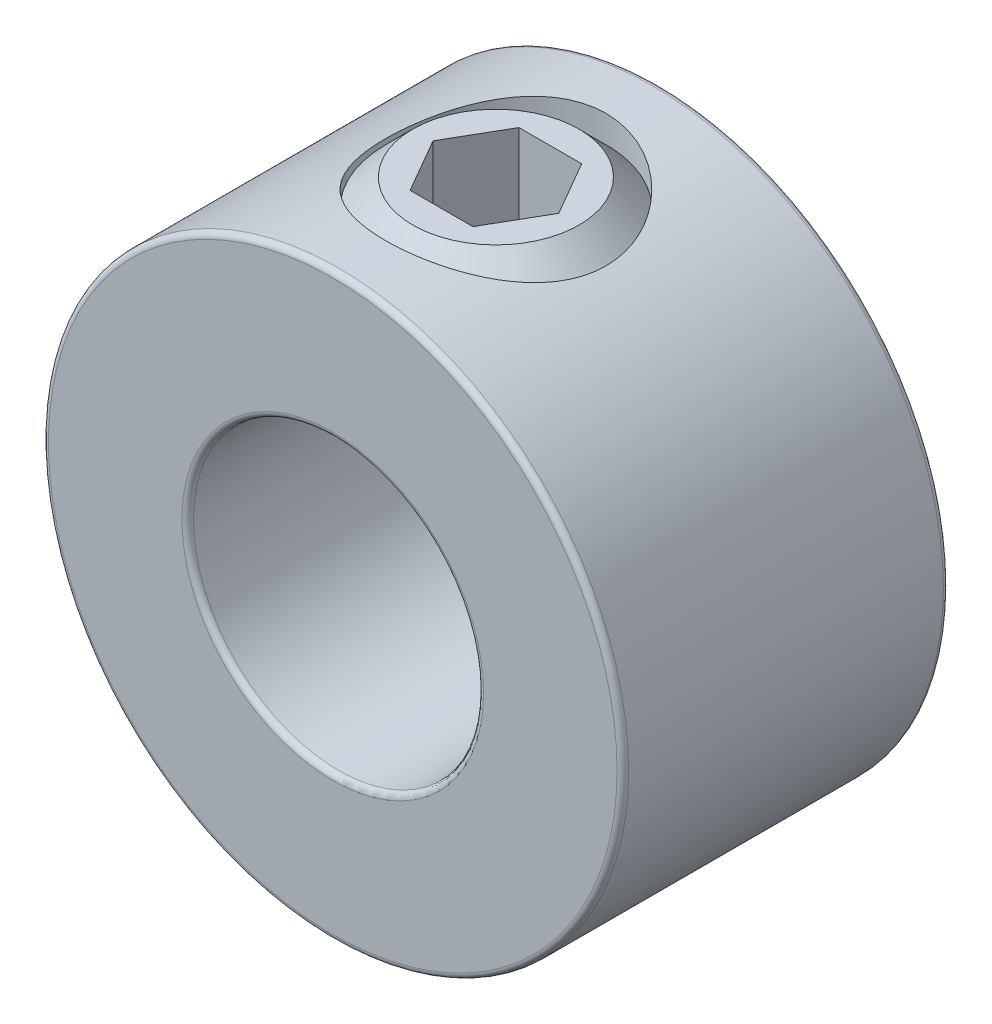
SolidWorks part; units mm, degrees
ref_plane "Front Plane" through (0, 0, 0) normal (0, 0, 1) x (1, 0, 0)
ref_plane "Top Plane" through (0, 0, 0) normal (0, 1, 0) x (1, 0, 0)
ref_plane "Right Plane" through (0, 0, 0) normal (1, 0, 0) x (0, 0, -1)
sketch "Sketch1" plane through (0, 0, 0) normal (0, 0, 1) x (1, 0, 0)
  circle A0 centre (0, 0) radius 6.35
  circle A1 centre (0, 0) radius 3.175
  point P4 (6.35, 0)
  dimension "Bore Dia" = 6.35
  dimension "OD" = 12.7
extrude "Extrude1" add sketch "Sketch1" along normal mid plane 7.1437
sketch "Sketch2" plane through (41.275, 0, 0) normal (0, -1, 0) x (0, 0, -1)
  line L0 (3.5719, -41.275) -> (-3.5719, -41.275) construction
  line L1 (-3.5719, -34.925) -> (-3.5719, -47.625) construction
  line L2 (3.5719, -47.625) -> (3.5719, -34.925) construction
  circle A0 centre (0, -41.275) radius 2.413
  point P7 (0, -43.688)
  dimension "Set Screw Dia" = 4.826
extrude "Cut-Extrude1" cut sketch "Sketch2" against normal through all
fillet "Fillet1" radius 0.127 4 edges at (3.175, 0, -3.5719) (3.175, 0, 3.5719) (6.35, 0, -3.5719) (6.35, 0, 3.5719)
sketch "Sketch3" plane through (0, 0, 0) normal (0, 0, 1) x (1, 0, 0)
  line L0 (-1.8198, 3.175) -> (-0.7119, 3.175)
  line L1 (0, 3.8869) -> (-0.7119, 3.175)
  line L2 (0, 3.8869) -> (0, 6.35)
  line L3 (0, 6.35) -> (-1.8198, 6.35)
  line L4 (-2.413, 3.7682) -> (-2.413, 5.7568)
  line L5 (0, 3.175) -> (0, 0) construction
  line L6 (-2.413, 3.7682) -> (-2.413, 3.175) construction
  line L7 (-2.413, 3.175) -> (-1.8198, 3.175) construction
  line L8 (-2.413, 5.7568) -> (-2.413, 6.35) construction
  line L9 (-1.8198, 3.175) -> (-2.413, 3.7682)
  line L10 (-2.413, 5.7568) -> (-1.8198, 6.35)
  line L11 (-2.413, 6.35) -> (-1.8198, 6.35) construction
  line L12 (-0.7119, 3.175) -> (0, 3.175) construction
  line L13 (0, 3.175) -> (0, 3.8869) construction
  circle A1 centre (0, 0) radius 3.175 construction
  dimension "D1" = 0.7119
  dimension "D2" = 0.5932
  dimension "Screw Length" = 3.175
revolve "Revolve1" add sketch "Sketch3" angle 360 about L5
sketch "Sketch4" plane through (3.3734, 6.35, 0) normal (0, -1, 0) x (0, 0, -1)
  line L1 (0, -1.9986) -> (-1.1906, -2.686)
  line L2 (-1.1906, -2.686) -> (-1.1906, -4.0608)
  line L3 (-1.1906, -4.0608) -> (0, -4.7483)
  line L4 (0, -4.7483) -> (1.1906, -4.0608)
  line L5 (1.1906, -4.0608) -> (1.1906, -2.686)
  line L6 (1.1906, -2.686) -> (0, -1.9986)
  circle A0 centre (0, -3.3734) radius 1.1906 construction
  circle A1 centre (0, -3.3734) radius 1.3748 construction
  dimension "D1" = 2.7496
  dimension "Hex Size" = 2.3813
extrude "Cut-Extrude2" cut sketch "Sketch4" along normal blind 2.3813
equation "\"D1@Fillet1\" = \"OD@Sketch1\"*.01"
equation "\"D1@Cut-Extrude2\" = \"Hex Size@Sketch4\""
equation "\"D2@Sketch3\" =(\"Set Screw Dia@Sketch2\"-\"D1@Sketch4\")/3.5"
equation "\"D1@Sketch3\" = \"D2@Sketch3\"*1.2"
